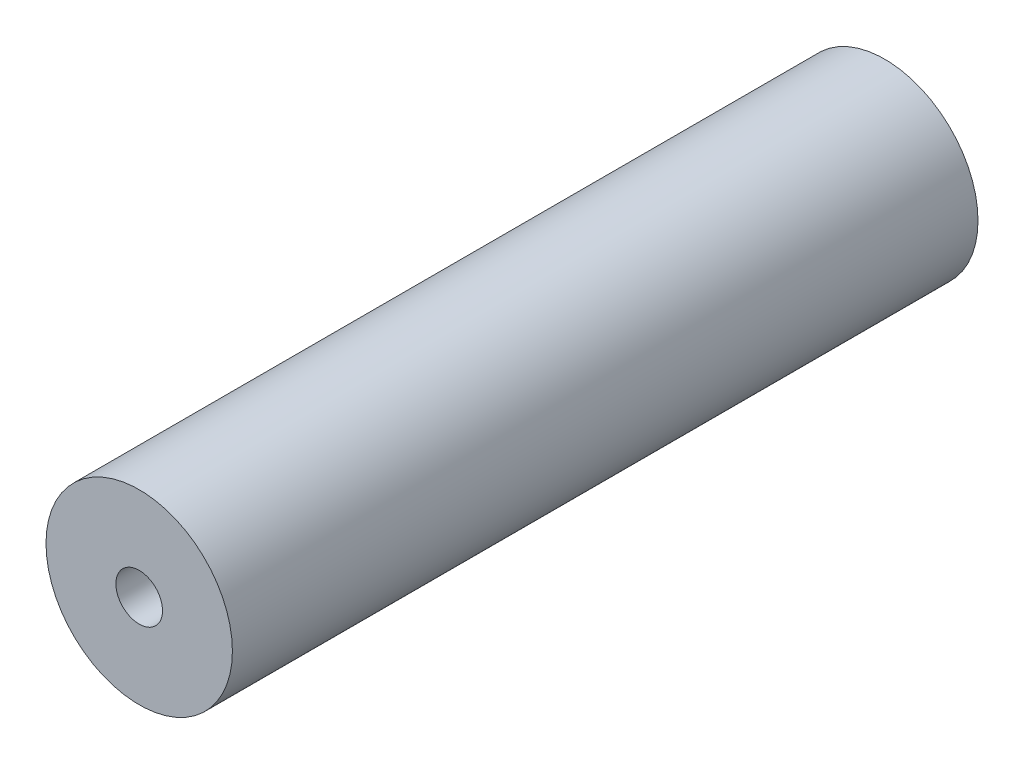
SolidWorks part; units mm, degrees
material "ASTM A36 Steel"
ref_plane "Front Plane" through (0, 0, 0) normal (0, 0, 1) x (1, 0, 0)
ref_plane "Top Plane" through (0, 0, 0) normal (0, 1, 0) x (1, 0, 0)
ref_plane "Right Plane" through (0, 0, 0) normal (1, 0, 0) x (0, 0, -1)
sketch "Sketch1" plane through (0, 0, 0) normal (0, 0, 1) x (1, 0, 0)
  circle A0 centre (0, 0) radius 38.1
  circle A1 centre (0, 0) radius 9.525
  dimension "D1" = 19.05
  dimension "D2" = 76.2
extrude "Boss-Extrude1" add sketch "Sketch1" along normal blind 304.8
